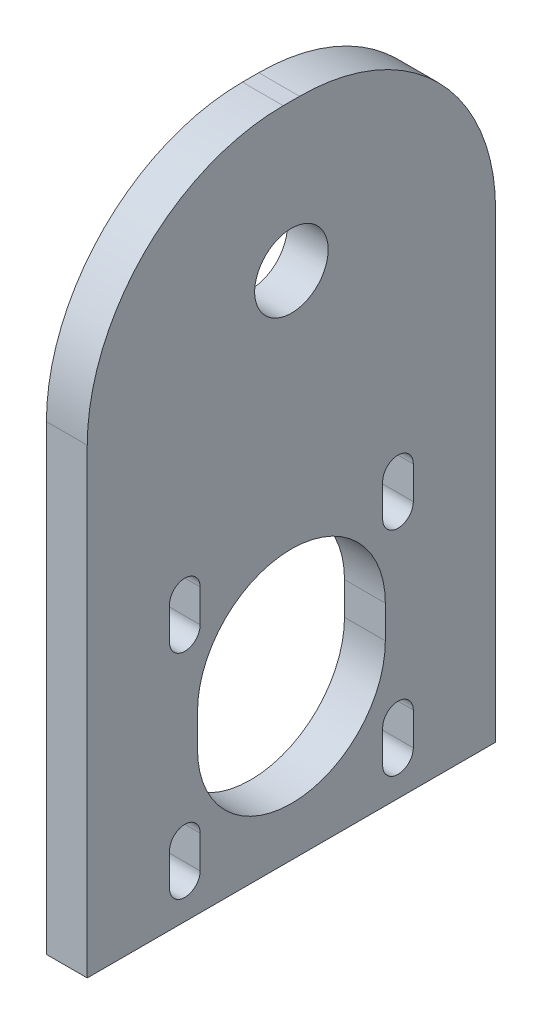
SolidWorks part; units mm, degrees
ref_plane "Front Plane" through (0, 0, 0) normal (0, 0, 1) x (1, 0, 0)
ref_plane "Top Plane" through (0, 0, 0) normal (0, 1, 0) x (1, 0, 0)
ref_plane "Right Plane" through (0, 0, 0) normal (1, 0, 0) x (0, 0, -1)
sketch "Sketch1" plane through (0, 0, 0) normal (1, 0, 0) x (0, 0, -1)
  line L0 (27.8734, -61.3086) -> (27.8734, -26.3086) construction
  line L1 (9.3734, 19.1914) -> (11.3734, 19.1914)
  line L2 (-14.6266, -4.8086) -> (-14.6266, -61.3086)
  line L3 (-14.6266, -61.3086) -> (35.3734, -61.3086)
  line L4 (35.3734, -4.8086) -> (35.3734, -61.3086)
  line L5 (27.8734, -26.3086) -> (-7.1266, -26.3086) construction
  line L6 (-7.1266, -26.3086) -> (-7.1266, -61.3086) construction
  line L7 (-2.6766, -30.7586) -> (23.4234, -30.7586) construction
  line L8 (-2.6766, -30.7586) -> (-2.6766, -56.8586) construction
  line L9 (-7.1266, -43.8086) -> (10.3734, -43.8086) construction
  line L10 (10.3734, -43.8086) -> (27.8734, -43.8086) construction
  line L11 (10.3734, -26.3086) -> (10.3734, -43.8086) construction
  line L12 (10.3734, -43.8086) -> (10.3734, -61.3086) construction
  line L13 (10.3734, -28.8086) -> (10.3734, 1.1914) construction
  line L14 (-4.5516, -26.7586) -> (-4.5516, -30.7586)
  line L15 (-0.8016, -26.7586) -> (-0.8016, -30.7586)
  line L16 (21.5484, -26.7586) -> (21.5484, -30.7586)
  line L17 (25.2984, -26.7586) -> (25.2984, -30.7586)
  line L18 (25.2984, -52.8586) -> (25.2984, -56.8586)
  line L19 (21.5484, -52.8586) -> (21.5484, -56.8586)
  line L20 (-4.5516, -52.8586) -> (-4.5516, -56.8586)
  line L21 (-0.8016, -52.8586) -> (-0.8016, -56.8586)
  line L22 (-1.1266, -39.8086) -> (-1.1266, -43.8086)
  line L23 (21.8734, -39.8086) -> (21.8734, -43.8086)
  line L24 (23.4234, -30.7586) -> (23.4234, -56.8586) construction
  line L25 (23.4234, -56.8586) -> (-2.6766, -56.8586) construction
  arc A0 (-1.1266, -43.8086) -> (21.8734, -43.8086) centre (10.3734, -43.8086) ccw
  arc A1 (-4.5516, -30.7586) -> (-0.8016, -30.7586) centre (-2.6766, -30.7586) ccw
  arc A2 (21.5484, -30.7586) -> (25.2984, -30.7586) centre (23.4234, -30.7586) ccw
  arc A3 (21.5484, -56.8586) -> (25.2984, -56.8586) centre (23.4234, -56.8586) ccw
  arc A4 (-4.5516, -56.8586) -> (-0.8016, -56.8586) centre (-2.6766, -56.8586) ccw
  circle A5 centre (10.3734, -43.8086) radius 15 construction
  circle A7 centre (10.3734, 1.1914) radius 4.5
  arc A8 (11.3734, 19.1914) -> (35.3734, -4.8086) centre (11.3734, -4.8086) cw
  arc A9 (9.3734, 19.1914) -> (-14.6266, -4.8086) centre (9.3734, -4.8086) ccw
  circle A10 centre (10.3734, 1.1914) radius 30 construction
  arc A11 (-0.8016, -26.7586) -> (-4.5516, -26.7586) centre (-2.6766, -26.7586) ccw
  arc A12 (25.2984, -26.7586) -> (21.5484, -26.7586) centre (23.4234, -26.7586) ccw
  arc A13 (25.2984, -52.8586) -> (21.5484, -52.8586) centre (23.4234, -52.8586) ccw
  arc A14 (-0.8016, -52.8586) -> (-4.5516, -52.8586) centre (-2.6766, -52.8586) ccw
  arc A15 (21.8734, -39.8086) -> (-1.1266, -39.8086) centre (10.3734, -39.8086) ccw
  point P27 (10.3734, -43.8086)
  dimension "D5" = 13.05
  dimension "D9" = 3.75
  dimension "D11" = 30
  dimension "D12" = 24
  dimension "D13" = 9
  dimension "D15" = 60
  dimension "D17" = 23
  dimension "D1" = 50
  dimension "D2" = 35
  dimension "D3" = 35
  dimension "D4" = 7.5
  dimension "D6" = 4
  dimension "D7" = 26.1
  dimension "D8" = 13.05
  dimension "D14" = 18
  dimension "D18" = 4
  dimension "D16" = 2
  dimension "D10" = 4
extrude "Boss-Extrude1" add sketch "Sketch1" along normal blind 5
sketch "Sketch2" plane through (0, -61.3086, 0) normal (0, -1, 0) x (-1, 0, 0)
  line L0 (-2.5, 35.3734) -> (-2.5, -14.6266) construction
  line L1 (-5, 35.3734) -> (0, 35.3734) construction
  line L2 (-5, -14.6266) -> (0, -14.6266) construction
  line L3 (0, 21.5484) -> (0, 25.2984) construction
  line L4 (0, -4.5516) -> (0, -0.8016) construction
  circle A0 centre (-2.5, -10.6266) radius 1.4
  circle A1 centre (-2.5, 31.3734) radius 1.4
  dimension "D1" = 4
  dimension "D2" = 4
  dimension "D3" = 2.8
extrude "Cut-Extrude1" cut sketch "Sketch2" against normal blind 10
